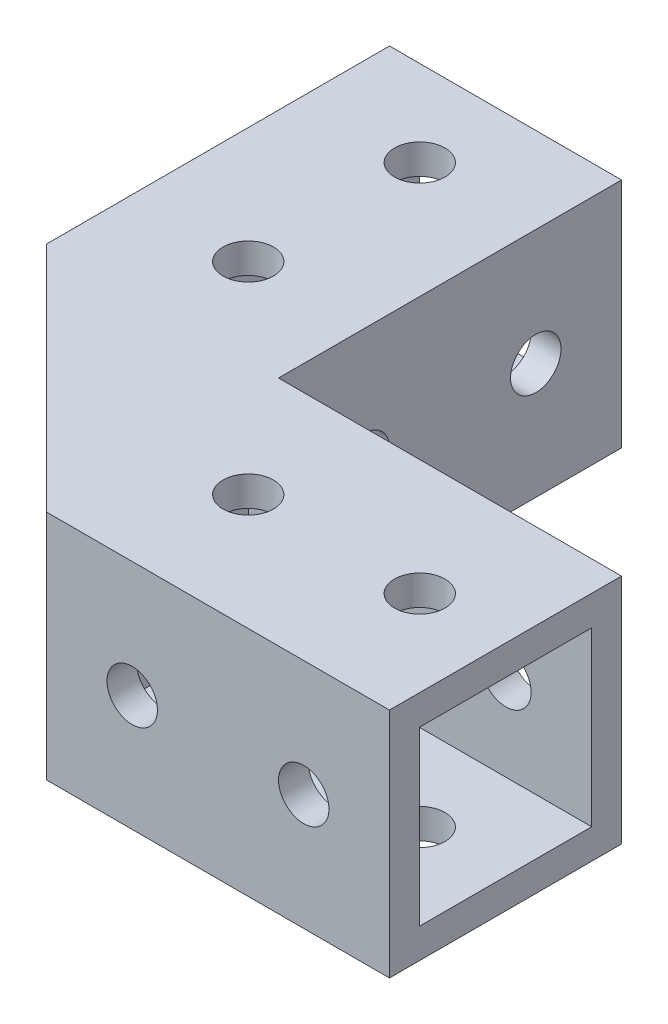
SolidWorks part; units mm, degrees
ref_plane "Front Plane" through (0, 0, 0) normal (0, 0, 1) x (1, 0, 0)
ref_plane "Top Plane" through (0, 0, 0) normal (0, 1, 0) x (1, 0, 0)
ref_plane "Right Plane" through (0, 0, 0) normal (1, 0, 0) x (0, 0, -1)
other "Configuration Table"
sketch "sketch1" plane through (0, 0, 0) normal (0, 1, 0) x (1, 0, 0)
  line L0 (0, -11.5) -> (8.5, -11.5) construction
  line L1 (0, 0) -> (34, 0)
  line L2 (0, 0) -> (0, -23)
  line L3 (0, -23) -> (34, -23)
  line L4 (34, 0) -> (34, -23)
  line L5 (8.5, -11.5) -> (25.5, -11.5) construction
  circle A1 centre (8.5, -11.5) radius 2.5
  circle A2 centre (25.5, -11.5) radius 2.5
  dimension "D4" = 5
  dimension "D1" = 23
  dimension "D2" = 34
  dimension "D3" = 8.5
  dimension "D6" = 17
  dimension "D5" = 2
extrude "Boss-Extrude1" add sketch "sketch1" along normal blind 23
sketch "Sketch6" plane through (0, 0, 0) normal (0, 0, -1) x (-1, 0, 0)
  line L0 (-34, 11.5) -> (-25.5, 11.5) construction
  line L1 (-25.5, 11.5) -> (-8.5, 11.5) construction
  line L4 (-34, 0) -> (0, 0)
  line L5 (0, 0) -> (0, 23)
  line L6 (0, 23) -> (-34, 23)
  line L7 (-34, 23) -> (-34, 0)
  line L8 (-34, 0) -> (0, 0)
  line L9 (0, 0) -> (0, 23)
  line L10 (0, 23) -> (-34, 23)
  line L11 (-34, 23) -> (-34, 0)
  circle A0 centre (-25.5, 11.5) radius 2.5
  circle A1 centre (-8.5, 11.5) radius 2.5
  dimension "D3" = 5
  dimension "D2" = 8.5
  dimension "D5" = 17
  dimension "D4" = 2
extrude "Cut-Extrude10" cut sketch "Sketch6" against normal through all flip side to cut
sketch "Sketch7" plane through (34, 0, 0) normal (1, 0, 0) x (0, 0, -1)
  line L0 (-23, 11.5) -> (0, 11.5) construction
  line L4 (-23, 0) -> (0, 0)
  line L5 (0, 0) -> (0, 23)
  line L6 (0, 23) -> (-23, 23)
  line L7 (-23, 23) -> (-23, 0)
  line L8 (-23, 0) -> (0, 0)
  line L9 (0, 0) -> (0, 23)
  line L10 (0, 23) -> (-23, 23)
  line L11 (-23, 23) -> (-23, 0)
  line L14 (-20.04, 20.04) -> (-2.96, 20.04)
  line L15 (-20.04, 20.04) -> (-20.04, 2.96)
  line L16 (-20.04, 2.96) -> (-2.96, 2.96)
  line L17 (-2.96, 20.04) -> (-2.96, 2.96)
  line L18 (-20.04, 20.04) -> (-2.96, 2.96) construction
  line L19 (-20.04, 2.96) -> (-2.96, 20.04) construction
  point P6 (-11.5, 11.5)
  dimension "D2" = 17.08
extrude "Cut-Extrude11" cut sketch "Sketch7" against normal blind 34 flip side to cut
sketch "Sketch9" plane through (0, 0, 0) normal (0, 1, 0) x (1, 0, 0)
  line L0 (0, 0) -> (34, 0) construction
  line L1 (0, 0) -> (24.0416, 24.0416) construction
  dimension "D1" = 45
ref_plane "Plane2" through (0, 0, 0) normal (-0.7071, 0, -0.7071) x (-0.7071, 0, 0.7071)
mirror "Mirror6" about plane through (0, 0, 0) normal (-0.7071, 0, -0.7071) of bodies 118 110
sketch "Sketch11" plane through (0, 0, 0) normal (0, 1, 0) x (1, 0, 0)
  line L0 (-23, 0) -> (0, -23)
  line L1 (0, 0) -> (-23, 0) construction
  line L2 (0, 0) -> (0, -23) construction
  line L3 (0, 0) -> (-23, 0)
  line L4 (0, 0) -> (0, -23)
extrude "Boss-Extrude2" add sketch "Sketch11" along normal blind 23
sketch "Sketch13" plane through (0, 0, 0) normal (0, 1, 0) x (1, 0, 0)
  line L0 (-11.5, 8.5) -> (5.1708, 5.1708) construction
  line L1 (0, 0) -> (24.0416, 24.0416) construction
  line L2 (5.1708, 5.1708) -> (8.5, -11.5) construction
  line L4 (8.7064, 8.7064) -> (0, 17)
  line L5 (0, 34) -> (0, 0) construction
  line L6 (8.7064, 8.7064) -> (17, 0)
  line L7 (0, 0) -> (34, 0) construction
  line L8 (0, 0) -> (24.0416, 24.0416) construction
  line L9 (0, 17) -> (0, 0)
  line L10 (0, 0) -> (17, 0)
  circle A0 centre (8.5, -11.5) radius 2.5 construction
  circle A1 centre (-11.5, 8.5) radius 2.5 construction
  circle A2 centre (8.5, -11.5) radius 2.5 construction
  circle A3 centre (-11.5, 8.5) radius 2.5 construction
  circle A4 centre (5.1708, 5.1708) radius 2.5
  dimension "D3" = 5
  dimension "D2" = 5
  dimension "D1" = 17
  dimension "D4" = 17
extrude "Boss-Extrude3" add sketch "Sketch13" along normal blind 4
equation "\"D2@sketch1\" = \"length\""
equation "\"holes\"= 2'Holes per side"
equation "\"cdist\"= 17mm'centre distance between holes"
equation "\"width\"= \"insetwidth\" + 2 * \"shellwidth\""
equation "\"length\"= \"cdist\" * \"holes\""
equation "\"D1@sketch1\"=\"width\""
equation "\"hdiam\"= 5mm'Hole diametre"
equation "\"D4@sketch1\" = \"hdiam\""
equation "\"D6@sketch1\" = \"cdist\""
equation "\"D5@sketch1\" = \"holes\""
equation "\"D2@Sketch6\"=\"cdist\"/2"
equation "\"D3@Sketch6\"=\"hdiam\""
equation "\"D5@Sketch6\"=\"cdist\""
equation "\"D4@Sketch6\"=\"holes\""
equation "\"D1@Boss-Extrude1\"=\"width\""
equation "\"joint\"= 90"
equation "\"D1@Sketch9\"=\"joint\"/2"
equation "\"D1@Boss-Extrude2\"=\"width\""
equation "\"D2@Sketch13\"=\"hdiam\""
equation "\"D4@Sketch13\"=\"cdist\""
equation "\"D1@Boss-Extrude3\"=\"supportheight\""
equation "\"supportheight\"= 4mm"
equation "\"tolerance\"= 0.04mm"
equation "\"insetwidth\"= 17mm"
equation "\"D1@Cut-Extrude11\"=\"length\""
equation "\"true\"= 1"
equation "\"false\"= 0"
equation "\"supportenabled\"= \"true\""
equation "\"Boss-Extrude3\"= IIF ( \"supportenabled\" < \"true\" , \"suppressed\" , \"unsuppressed\" )"
equation "\"D2@Sketch7\"=\"insetwidth\"+\"tolerance\"*2"
equation "\"shellwidth\"= 3mm"
